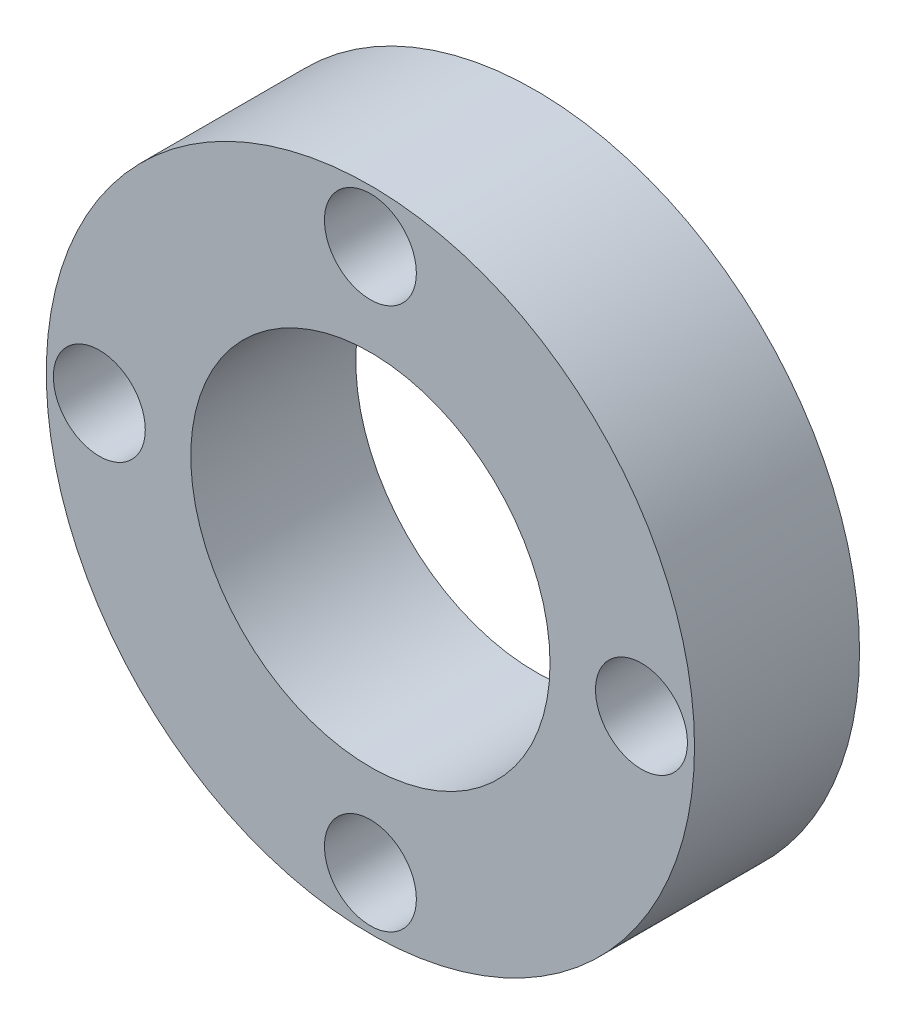
SolidWorks part; units mm, degrees
ref_plane "Front Plane" through (0, 0, 0) normal (0, 0, 1) x (1, 0, 0)
ref_plane "Top Plane" through (0, 0, 0) normal (0, 1, 0) x (1, 0, 0)
ref_plane "Right Plane" through (0, 0, 0) normal (1, 0, 0) x (0, 0, -1)
sketch "Sketch1" plane through (0, 0, 0) normal (0, 0, 1) x (1, 0, 0)
  circle A0 centre (0, 0) radius 13.75
  circle A1 centre (0, 0) radius 7.62
  dimension "D1" = 27.5
  dimension "D2" = 15.24
  dimension "D3" = 6.13
extrude "Boss-Extrude1" add sketch "Sketch1" against normal blind 7
sketch "Sketch3" plane through (0, 0, 0) normal (0, 0, 1) x (1, 0, 0)
  line L0 (0, 13.75) -> (0, -13.75) construction
  line L1 (-13.75, 0) -> (13.75, 0) construction
  circle A0 centre (0, 0) radius 13.75 construction
  circle A1 centre (-11.5, 0) radius 1.95
  circle A2 centre (0, 11.5) radius 1.95
  circle A3 centre (11.5, 0) radius 1.95
  circle A4 centre (0, -11.5) radius 1.95
  dimension "D2" = 3.9
  dimension "D4" = 3.9
  dimension "D5" = 3.9
  dimension "D6" = 3.9
  dimension "D1" = 11.5
  dimension "D3" = 11.5
  dimension "D7" = 11.5
  dimension "D8" = 11.5
extrude "Cut-Extrude1" cut sketch "Sketch3" against normal up to next
